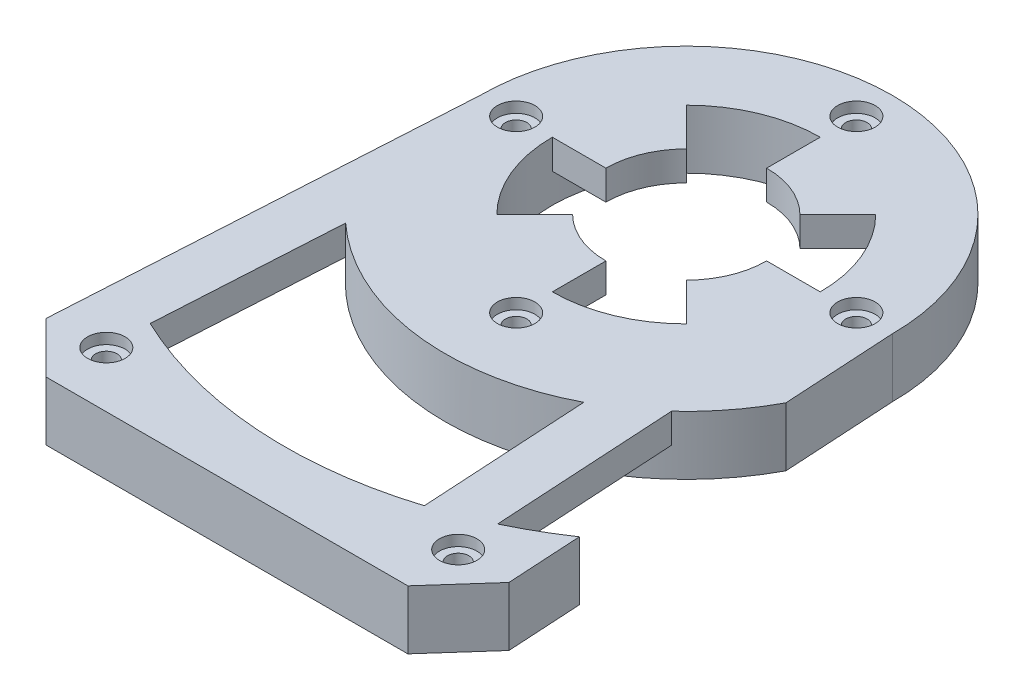
SolidWorks part; units mm, degrees
ref_plane "Front Plane" through (0, 0, 0) normal (0, 0, 1) x (1, 0, 0)
ref_plane "Top Plane" through (0, 0, 0) normal (0, 1, 0) x (1, 0, 0)
ref_plane "Right Plane" through (0, 0, 0) normal (1, 0, 0) x (0, 0, -1)
sketch "Sketch1" plane through (0, 0, 0) normal (0, 1, 0) x (1, 0, 0)
  circle A0 centre (0, 0) radius 38.5
  dimension "D1" = 77
extrude "Boss-Extrude1" add sketch "Sketch1" along normal blind 11
sketch "Sketch2" plane through (0, 11, 0) normal (0, 1, 0) x (1, 0, 0)
  line L0 (0, 0) -> (0, -86) construction
  line L1 (-43.5, -86) -> (43.5, -86) construction
  line L2 (-38.5, 0) -> (-43.5, -86) construction
  line L3 (38.5, 0) -> (43.5, -86) construction
  line L4 (-38.5, 0) -> (-43.5, -86)
  line L5 (-43.5, -86) -> (43.5, -86)
  line L6 (43.5, -86) -> (38.5, 0)
  circle A0 centre (0, 0) radius 38.5 construction
  arc A1 (-38.5, 0) -> (38.5, 0) centre (0, 0) ccw
  point P5 (0, -86)
  dimension "D1" = 86
  dimension "D2" = 87
extrude "Boss-Extrude2" add sketch "Sketch2" against normal through all
chamfer "Chamfer1" distance 10 angle 45 2 edges at (43.5, 5.5, 86) (-43.5, 5.5, 86)
sketch "Sketch3" plane through (0, 11, 0) normal (0, 1, 0) x (1, 0, 0)
  circle A0 centre (0, 0) radius 15
  dimension "D1" = 30
extrude "Cut-Extrude1" cut sketch "Sketch3" against normal through all
sketch "Sketch4" plane through (0, 0, 0) normal (0, -1, 0) x (1, 0, 0)
  circle A0 centre (0, 0) radius 25
  dimension "D1" = 50
extrude "Cut-Extrude2" cut sketch "Sketch4" against normal blind 5.5
sketch "Sketch5" plane through (0, 11, 0) normal (0, 1, 0) x (1, 0, 0)
  line L0 (25, 0) -> (15, 0)
  line L1 (0, 25) -> (0, 15)
  line L6 (-17.6777, 17.6777) -> (-10.6066, 10.6066)
  line L7 (17.6777, 17.6777) -> (10.6066, 10.6066)
  line L8 (10.6066, -10.6066) -> (17.6777, -17.6777)
  line L9 (-15, 0) -> (-25, 0)
  line L10 (-10.6066, -10.6066) -> (-17.6777, -17.6777)
  line L11 (0, -15) -> (0, -25)
  arc A4 (-25, 0) -> (-17.6777, -17.6777) centre (0, 0) ccw
  arc A5 (-15, 0) -> (-10.6066, -10.6066) centre (0, 0) ccw
  arc A6 (0, 15) -> (-10.6066, 10.6066) centre (0, 0) ccw
  arc A7 (0, 25) -> (-17.6777, 17.6777) centre (0, 0) ccw
  arc A8 (15, 0) -> (10.6066, 10.6066) centre (0, 0) ccw
  arc A9 (25, 0) -> (17.6777, 17.6777) centre (0, 0) ccw
  arc A10 (0, -15) -> (10.6066, -10.6066) centre (0, 0) ccw
  arc A11 (0, -25) -> (17.6777, -17.6777) centre (0, 0) ccw
  dimension "D1" = 50
  dimension "D2" = 45
  dimension "D3" = 45
extrude "Cut-Extrude3" cut sketch "Sketch5" against normal blind 5.5
sketch "Sketch7" plane through (0, 0, 0) normal (0, 1, 0) x (1, 0, 0)
  line L13 (-33.5, -86) -> (34.0335, -86)
  line L14 (34.0335, -86) -> (42.9196, -76.0169)
  line L15 (42.9196, -76.0169) -> (38.5, 0)
  line L16 (-38.5, 0) -> (-42.9505, -76.5495)
  line L17 (-42.9505, -76.5495) -> (-33.5, -86)
  line L20 (42.1083, -62.0636) -> (39.7287, -21.1336)
  line L21 (-39.7287, -21.1336) -> (-42.1083, -62.0636)
  arc A0 (-39.7287, -21.1336) -> (39.7287, -21.1336) centre (0, 0) ccw
  arc A1 (-42.1083, -62.0636) -> (42.1083, -62.0636) centre (0, 0) ccw
  arc A3 (38.5, 0) -> (-38.5, 0) centre (0, 0) ccw
  dimension "D1" = 90
  dimension "D2" = 150
  dimension "D4" = 0
extrude "Cut-Extrude5" cut sketch "Sketch7" along normal blind 5.5
sketch "Sketch8" plane through (0, 11, 0) normal (0, 1, 0) x (1, 0, 0)
  line L0 (-30.4115, -33.1684) -> (-32.4153, -67.6332)
  line L1 (-38.5, 0) -> (-42.9505, -76.5495) construction
  line L2 (20.7867, -39.9113) -> (22.6236, -71.5065)
  line L3 (42.9196, -76.0169) -> (38.5, 0) construction
  arc A0 (-30.4115, -33.1684) -> (20.7867, -39.9113) centre (0, 0) ccw
  arc A1 (-32.4153, -67.6332) -> (22.6236, -71.5065) centre (0, 0) ccw
  dimension "D1" = 90
  dimension "D2" = 150
  dimension "D3" = 10
  dimension "D4" = 20
extrude "Cut-Extrude6" cut sketch "Sketch8" against normal blind 5.5
sketch "Sketch9" plane through (0, 11, 0) normal (0, 1, 0) x (1, 0, 0)
  line L0 (0, 25) -> (0, 38.5) construction
  circle A0 centre (0, 0) radius 31.75 construction
  arc A1 (38.5, 0) -> (-38.5, 0) centre (0, 0) ccw construction
  circle A2 centre (-31.75, 0) radius 3.5
  circle A3 centre (0, 31.75) radius 3.5
  circle A4 centre (31.75, 0) radius 3.5
  circle A5 centre (0, -31.75) radius 3.5
  point P9 (0, 31.75)
  point P21 (0, 0)
  dimension "D1" = 7
  dimension "D2" = 4
extrude "Cut-Extrude7" cut sketch "Sketch9" against normal blind 2
sketch "Sketch10" plane through (0, 9, 0) normal (0, 1, 0) x (1, 0, 0)
  circle A0 centre (-31.75, 0) radius 2
  circle A1 centre (0, 31.75) radius 2
  circle A2 centre (31.75, 0) radius 2
  circle A3 centre (0, -31.75) radius 2
  point P12 (0, 0)
  dimension "D1" = 4
  dimension "D2" = 4
extrude "Cut-Extrude8" cut sketch "Sketch10" against normal through all
sketch "Sketch11" plane through (0, 5.5, 0) normal (0, -1, 0) x (1, 0, 0)
  line L0 (39.7287, 21.1336) -> (42.1083, 62.0636)
  line L1 (30.4115, 33.1684) -> (32.4153, 67.6332)
  line L2 (28.3872, -1.6504) -> (30.4115, 33.1684) construction
  circle A0 centre (0, 0) radius 28.4351 construction
  arc A1 (42.1083, 62.0636) -> (32.4153, 67.6332) centre (0, 0) ccw
  arc A2 (39.7287, 21.1336) -> (30.4115, 33.1684) centre (0, 0) ccw
  arc A3 (32.4153, 67.6332) -> (42.1083, 62.0636) centre (0, 0) ccw construction
  arc A4 (30.4115, 33.1684) -> (39.7287, 21.1336) centre (0, 0) ccw construction
  dimension "D1" = 10
extrude "Cut-Extrude9" cut sketch "Sketch11" against normal through all
sketch "Sketch13" plane through (0, 11, 0) normal (0, 1, 0) x (1, 0, 0)
  line L0 (-38.2253, -81.2747) -> (-27.0001, -69.9714) construction
  line L1 (-42.9505, -76.5495) -> (-33.5, -86) construction
  line L2 (27.2607, -69.8702) -> (38.4765, -81.0084) construction
  line L3 (34.0335, -86) -> (42.9196, -76.0169) construction
  circle A1 centre (-32.6127, -75.623) radius 2
  circle A2 centre (32.8686, -75.4393) radius 2
  dimension "D1" = 4
extrude "Cut-Extrude10" cut sketch "Sketch13" against normal through all
sketch "Sketch14" plane through (0, 11, 0) normal (0, 1, 0) x (1, 0, 0)
  circle A0 centre (-32.6127, -75.623) radius 3.5
  circle A1 centre (32.8686, -75.4393) radius 3.5
  dimension "D1" = 7
extrude "Cut-Extrude11" cut sketch "Sketch14" against normal up to surface (2 mm away) up to face at (-31.75, 9, 2)
